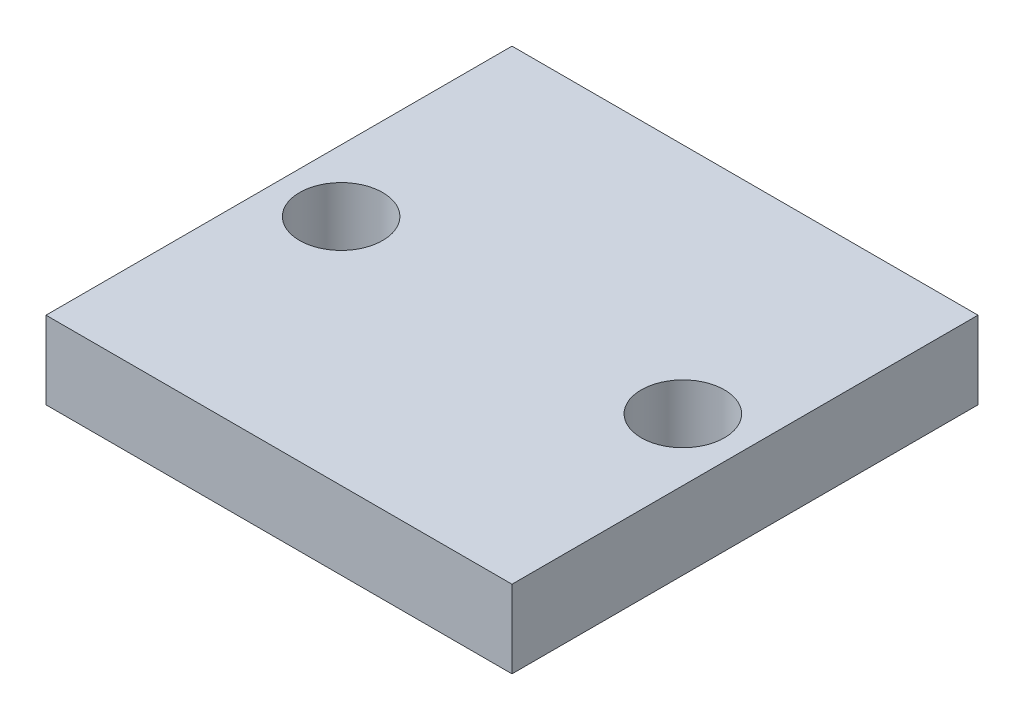
SolidWorks part; units mm, degrees
ref_plane "Front Plane" through (0, 0, 0) normal (0, 0, 1) x (1, 0, 0)
ref_plane "Top Plane" through (0, 0, 0) normal (0, 1, 0) x (1, 0, 0)
ref_plane "Right Plane" through (0, 0, 0) normal (1, 0, 0) x (0, 0, -1)
sketch "Sketch1" plane through (0, 0, 0) normal (0, 1, 0) x (1, 0, 0)
  line L1 (9.525, -9.525) -> (-9.525, -9.525)
  line L2 (9.525, -9.525) -> (9.525, 9.525)
  line L3 (9.525, 9.525) -> (-9.525, 9.525)
  line L4 (-9.525, -9.525) -> (-9.525, 9.525)
  line L5 (9.525, -9.525) -> (-9.525, 9.525) construction
  line L6 (9.525, 9.525) -> (-9.525, -9.525) construction
  point P0 (0, 0)
  dimension "D1" = 19.05
  dimension "D2" = 19.05
extrude "Boss-Extrude1" add sketch "Sketch1" along normal blind 3.175
hole_wizard "M3 Clearance Hole1" positions "Sketch2" profile "Sketch4" hole size "M3" standard "ANSI Metric"
sketch "Sketch2" plane through (0, 3.175, 0) normal (0, 1, 0) x (1, 0, 0)
  point P0 (6.985, 0)
  point P3 (-6.985, 0)
sketch "Sketch4" plane through (6.985, 3.175, 0) normal (1, 0, 0) x (0, 0, 1)
  line L0 (0, 0) -> (0, 8.6415)
  line L1 (0, 8.6415) -> (1.7, 7.62)
  line L2 (1.7, 7.62) -> (1.7, 0)
  line L5 (1.7, 0) -> (0, 0)
  line L10 (0, 8.6415) -> (-1.7, 7.62) construction
  line L11 (0, -6.35) -> (0, 107.95) construction
  dimension "Hole Dia." = 3.4
  dimension "Hole Depth" = 7.62
  dimension "Drill Angle" = 118
